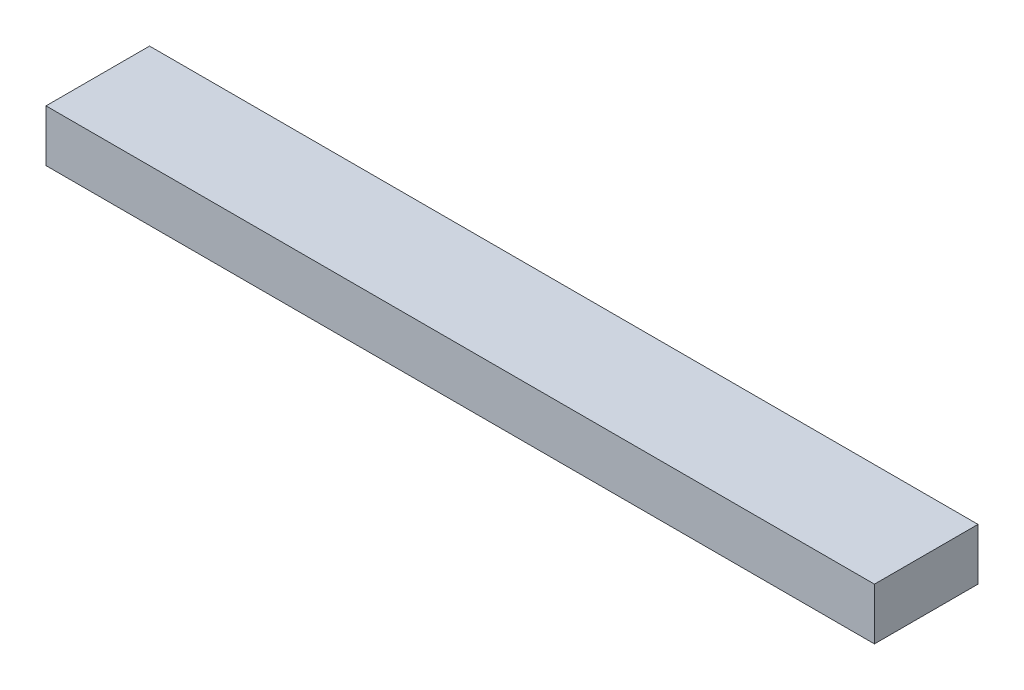
SolidWorks part; units mm, degrees
ref_plane "Front Plane" through (0, 0, 0) normal (0, 0, 1) x (1, 0, 0)
ref_plane "Top Plane" through (0, 0, 0) normal (0, 1, 0) x (1, 0, 0)
ref_plane "Right Plane" through (0, 0, 0) normal (1, 0, 0) x (0, 0, -1)
sketch "Sketch1" plane through (0, 0, 0) normal (1, 0, 0) x (0, 0, -1)
  line L1 (0, 0) -> (38.1, 0)
  line L2 (0, 0) -> (0, 19.05)
  line L3 (0, 19.05) -> (38.1, 19.05)
  line L4 (38.1, 0) -> (38.1, 19.05)
  dimension "D1" = 38.1
  dimension "D2" = 19.05
extrude "Boss-Extrude1" add sketch "Sketch1" along normal blind 304.8
